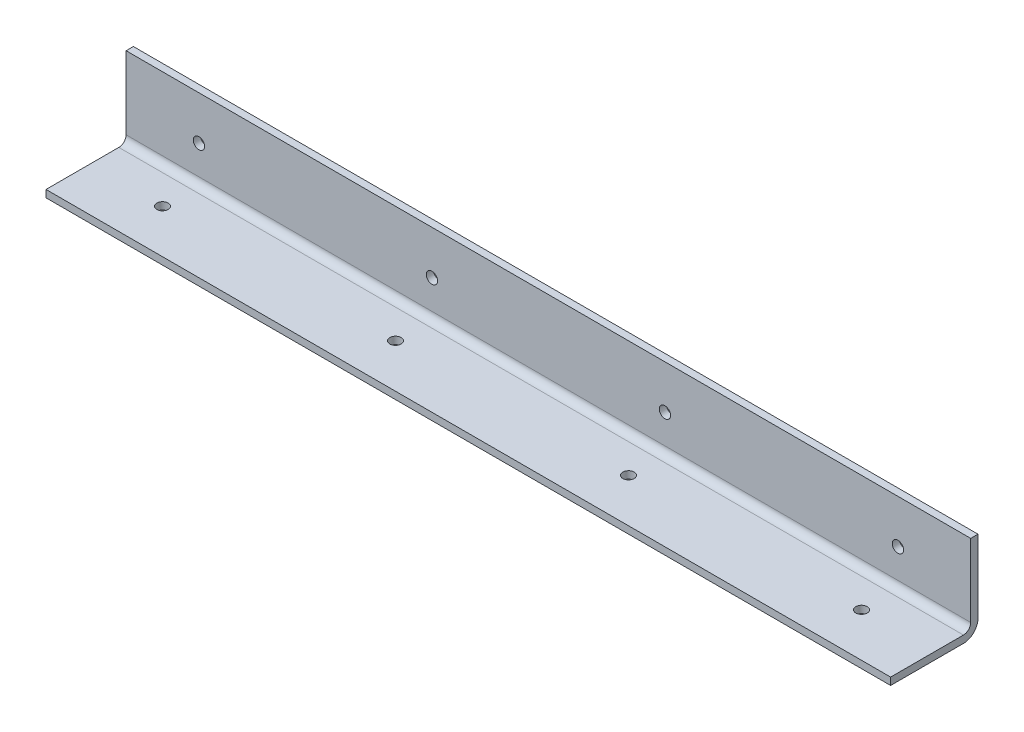
SolidWorks part; units mm, degrees
ref_plane "Front Plane" through (0, 0, 0) normal (0, 0, 1) x (1, 0, 0)
ref_plane "Top Plane" through (0, 0, 0) normal (0, 1, 0) x (1, 0, 0)
ref_plane "Right Plane" through (0, 0, 0) normal (1, 0, 0) x (0, 0, -1)
sketch "Sketch1" plane through (0, 0, 0) normal (1, 0, 0) x (0, 0, -1)
  line L0 (0, 38.1) -> (0, 0)
  line L1 (0, 0) -> (-38.1, 0)
  line L2 (-38.1, 0) -> (-38.1, 3.175)
  line L3 (-38.1, 3.175) -> (-3.175, 3.175)
  line L4 (-3.175, 3.175) -> (-3.175, 38.1)
  line L5 (-3.175, 38.1) -> (0, 38.1)
  dimension "D1" = 38.1
  dimension "D2" = 3.175
extrude "Boss-Extrude1" add sketch "Sketch1" along normal mid plane 368.3
fillet "Fillet1" radius 3.175 1 edges at (0, 3.175, 3.175)
fillet "Fillet2" radius 6.35 1 edges at (0, 0, 0)
sketch "Sketch2" plane through (0, 0, 0) normal (0, 0, -1) x (-1, 0, 0)
  line L0 (184.15, 6.35) -> (184.15, 38.1) construction
  line L1 (-184.15, 0) -> (184.15, 0) construction
  circle A0 centre (152.4, 19.05) radius 2.4638
  dimension "D1" = 31.75
  dimension "D3" = 4.9276
  dimension "D2" = 19.05
extrude "Cut-Extrude1" cut sketch "Sketch2" against normal through all
sketch "Sketch3" plane through (0, 0, 0) normal (0, -1, 0) x (1, 0, 0)
  line L0 (184.15, 38.1) -> (-184.15, 38.1) construction
  line L1 (-184.15, 38.1) -> (-184.15, 6.35) construction
  circle A0 centre (-152.4, 19.05) radius 2.4638
  dimension "D1" = 19.05
  dimension "D3" = 4.9276
  dimension "D2" = 31.75
extrude "Cut-Extrude2" cut sketch "Sketch3" against normal through all
pattern_linear "LPattern1" count 4 spacing 101.6 along (1, 0, 0) of "Cut-Extrude1", "Cut-Extrude2"
